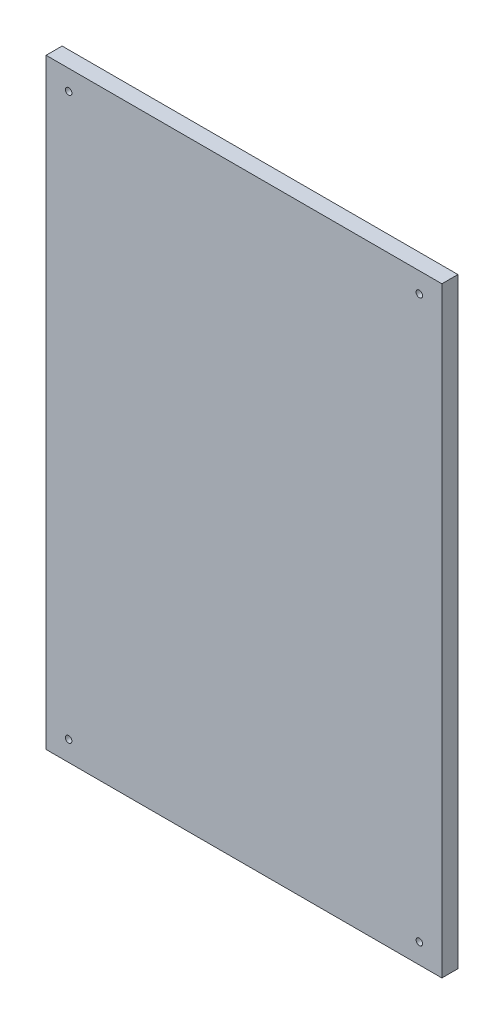
SolidWorks part; units mm, degrees
ref_plane "Front Plane" through (0, 0, 0) normal (0, 0, 1) x (1, 0, 0)
ref_plane "Top Plane" through (0, 0, 0) normal (0, 1, 0) x (1, 0, 0)
ref_plane "Right Plane" through (0, 0, 0) normal (1, 0, 0) x (0, 0, -1)
sketch "Sketch1" plane through (0, 0, 0) normal (0, 0, 1) x (1, 0, 0)
  line L1 (0, 0) -> (395, 0)
  line L2 (0, 0) -> (0, 600)
  line L3 (0, 600) -> (395, 600)
  line L4 (395, 0) -> (395, 600)
  dimension "D1" = 600
  dimension "D2" = 395
extrude "Boss-Extrude1" add sketch "Sketch1" along normal blind 16
sketch "Sketch2" plane through (0, 0, 16) normal (0, 0, 1) x (1, 0, 0)
  line L0 (197.5, 600) -> (197.5, 0) construction
  line L3 (395, 600) -> (0, 600) construction
  line L6 (0, 0) -> (395, 0) construction
  line L7 (22.5, 580) -> (372.5, 580) construction
  line L8 (395, 300) -> (0, 300) construction
  line L9 (395, 0) -> (395, 600) construction
  line L10 (0, 600) -> (0, 0) construction
  circle A0 centre (22.5, 580) radius 3.25
  circle A1 centre (372.5, 580) radius 3.25
  circle A2 centre (22.5, 20) radius 3.25
  circle A3 centre (372.5, 20) radius 3.25
  dimension "D1" = 6.5
  dimension "D2" = 350
  dimension "D3" = 175
  dimension "D4" = 20
extrude "Cut-Extrude1" cut sketch "Sketch2" against normal through all
equation "\"D2@Sketch2\"=50*7"
equation "\"D3@Sketch2\"=50*7/2"
